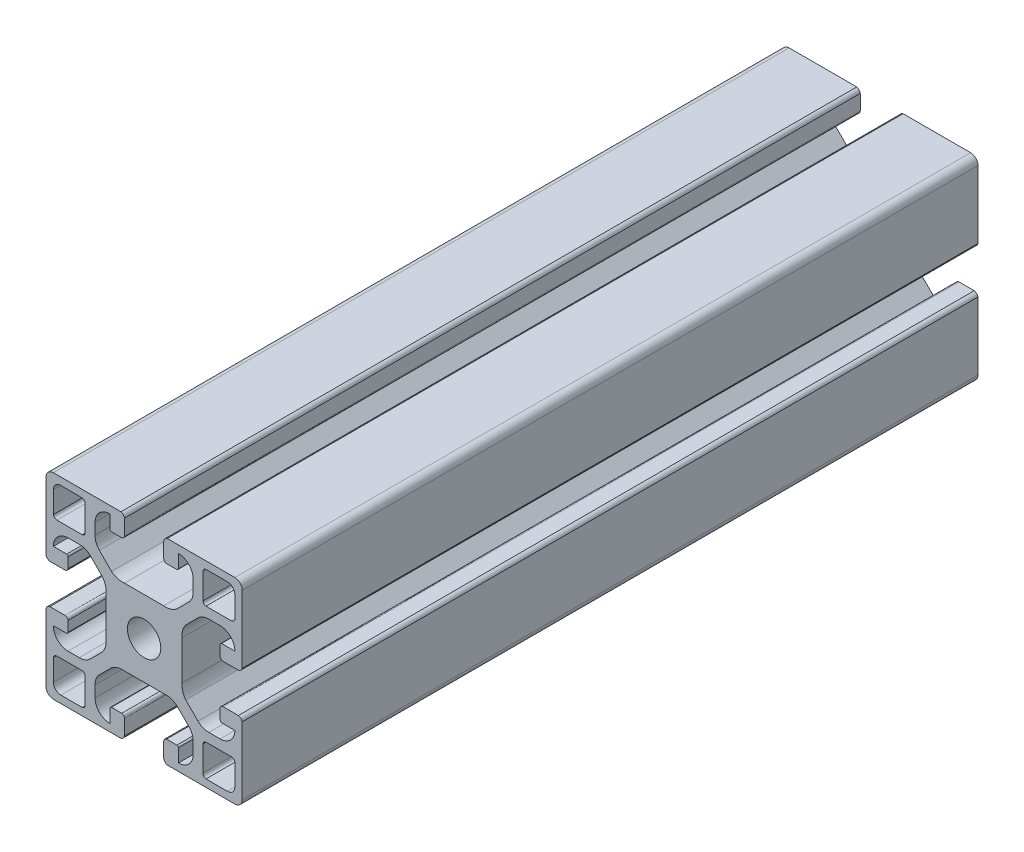
SolidWorks part; units mm, degrees
ref_plane "Alzado" through (0, 0, 0) normal (0, 0, 1) x (1, 0, 0)
ref_plane "Planta" through (0, 0, 0) normal (0, 1, 0) x (1, 0, 0)
ref_plane "Vista lateral" through (0, 0, 0) normal (1, 0, 0) x (0, 0, -1)
sketch "Croquis1" plane through (0, 0, 0) normal (0, 0, 1) x (1, 0, 0)
  line L9 (0, 18.5) -> (0, 4.7232)
  line L10 (0.7765, 4) -> (3.8765, 4)
  line L12 (12.25, -4.7232) -> (12.25, 4.7232)
  line L14 (4.5, 4.5616) -> (4.5, 6.6755)
  line L15 (4.2267, 7) -> (1.5, 7)
  line L17 (9.0164, 9.1211) -> (11.5076, 6.6299)
  line L18 (6.9331, 10) -> (4.5, 10)
  line L19 (40, -18.5) -> (40, -4.7232)
  line L20 (5.7166, 12) -> (7.3817, 12)
  line L21 (5.7166, 12) -> (2.23, 12)
  line L22 (1.5, 12.6183) -> (1.5, 17)
  line L23 (24.7232, 7.75) -> (15.2768, 7.75)
  line L24 (10.8789, 10.9836) -> (13.3701, 8.4924)
  line L25 (10, 13.0669) -> (10, 15.5)
  line L26 (13, 15.7733) -> (13, 18.5)
  line L27 (15.4384, 15.5) -> (13.3245, 15.5)
  line L28 (16, 19.2235) -> (16, 16.1235)
  line L29 (1.3293, 20) -> (15.2768, 20)
  line L30 (8, 14.2834) -> (8, 12.6183)
  line L31 (8, 14.2834) -> (8, 17.77)
  line L32 (7.3817, 18.5) -> (3, 18.5)
  line L33 (32.6183, 18.5) -> (37, 18.5)
  line L34 (32, 14.2834) -> (32, 17.77)
  line L35 (32, 14.2834) -> (32, 12.6183)
  line L36 (38.6707, 20) -> (24.7232, 20)
  line L37 (24, 19.2235) -> (24, 16.1235)
  line L38 (24.5616, 15.5) -> (26.6755, 15.5)
  line L39 (27, 15.7733) -> (27, 18.5)
  line L40 (30, 13.0669) -> (30, 15.5)
  line L41 (29.1211, 10.9836) -> (26.6299, 8.4924)
  line L42 (38.5, 12.6183) -> (38.5, 17)
  line L43 (34.2834, 12) -> (37.77, 12)
  line L44 (34.2834, 12) -> (32.6183, 12)
  line L45 (33.0669, 10) -> (35.5, 10)
  line L46 (30.9836, 9.1211) -> (28.4924, 6.6299)
  line L47 (35.7733, 7) -> (38.5, 7)
  line L48 (35.5, 4.5616) -> (35.5, 6.6755)
  line L49 (27.75, -4.7232) -> (27.75, 4.7232)
  line L51 (39.2235, 4) -> (36.1235, 4)
  line L52 (40, 18.5) -> (40, 4.7232)
  line L53 (39.2235, -4) -> (36.1235, -4)
  line L54 (35.5, -4.5616) -> (35.5, -6.6755)
  line L55 (35.7733, -7) -> (38.5, -7)
  line L56 (30.9836, -9.1211) -> (28.4924, -6.6299)
  line L57 (33.0669, -10) -> (35.5, -10)
  line L58 (34.2834, -12) -> (32.6183, -12)
  line L59 (34.2834, -12) -> (37.77, -12)
  line L60 (38.5, -12.6183) -> (38.5, -17)
  line L61 (29.1211, -10.9836) -> (26.6299, -8.4924)
  line L62 (30, -13.0669) -> (30, -15.5)
  line L63 (27, -15.7733) -> (27, -18.5)
  line L64 (24.5616, -15.5) -> (26.6755, -15.5)
  line L65 (24, -19.2235) -> (24, -16.1235)
  line L66 (38.6707, -20) -> (24.7232, -20)
  line L67 (32, -14.2834) -> (32, -12.6183)
  line L68 (32, -14.2834) -> (32, -17.77)
  line L69 (32.6183, -18.5) -> (37, -18.5)
  line L70 (7.3817, -18.5) -> (3, -18.5)
  line L71 (8, -14.2834) -> (8, -17.77)
  line L72 (8, -14.2834) -> (8, -12.6183)
  line L73 (1.3293, -20) -> (15.2768, -20)
  line L74 (16, -19.2235) -> (16, -16.1235)
  line L75 (15.4384, -15.5) -> (13.3245, -15.5)
  line L76 (13, -15.7733) -> (13, -18.5)
  line L77 (10, -13.0669) -> (10, -15.5)
  line L78 (10.8789, -10.9836) -> (13.3701, -8.4924)
  line L79 (24.7232, -7.75) -> (15.2768, -7.75)
  line L80 (1.5, -12.6183) -> (1.5, -17)
  line L81 (5.7166, -12) -> (2.23, -12)
  line L82 (5.7166, -12) -> (7.3817, -12)
  line L83 (6.9331, -10) -> (4.5, -10)
  line L84 (9.0164, -9.1211) -> (11.5076, -6.6299)
  line L85 (4.2267, -7) -> (1.5, -7)
  line L86 (4.5, -4.5616) -> (4.5, -6.6755)
  line L87 (0.7765, -4) -> (3.8765, -4)
  line L88 (0, -18.5) -> (0, -4.7232)
  arc A0 (4.5, 10) -> (1.5, 7) centre (4.5, 7) ccw
  arc A1 (10, 15.5) -> (13, 18.5) centre (13, 15.5) cw
  arc A2 (0, 18.5) -> (1.5, 20) centre (1.5, 18.5) cw
  arc A3 (1.5, 17) -> (3, 18.5) centre (3, 17) cw
  circle A4 centre (20, 0) radius 3.4
  arc A5 (38.5, 17) -> (37, 18.5) centre (37, 17) ccw
  arc A6 (40, 18.5) -> (38.5, 20) centre (38.5, 18.5) ccw
  arc A7 (30, 15.5) -> (27, 18.5) centre (27, 15.5) ccw
  arc A8 (35.5, 10) -> (38.5, 7) centre (35.5, 7) cw
  arc A9 (35.5, -10) -> (38.5, -7) centre (35.5, -7) ccw
  arc A10 (30, -15.5) -> (27, -18.5) centre (27, -15.5) cw
  arc A11 (40, -18.5) -> (38.5, -20) centre (38.5, -18.5) cw
  arc A12 (38.5, -17) -> (37, -18.5) centre (37, -17) cw
  arc A13 (1.5, -17) -> (3, -18.5) centre (3, -17) ccw
  arc A14 (0, -18.5) -> (1.5, -20) centre (1.5, -18.5) ccw
  arc A15 (10, -15.5) -> (13, -18.5) centre (13, -15.5) ccw
  arc A16 (4.5, -10) -> (1.5, -7) centre (4.5, -7) cw
  spline S0 degree 2 poles (6.7957, 10) (8.0801, 10.025) (9.0164, 9.1211) knots 0 0 0 1 1 1
  spline S1 degree 2 poles (11.5076, 6.6299) (12.3742, 5.4854) (12.25, 4) knots 0 0 0 1 1 1
  spline S2 degree 2 poles (0, 4.7232) (0.1682, 4.1542) (0.7765, 4) knots 0 0 0 1 1 1
  spline S3 degree 2 poles (3.8765, 4) (4.593, 4.0978) (4.5, 4.8884) knots 0 0 0 1 1 1
  spline S4 degree 2 poles (4.2267, 7) (4.4426, 6.908) (4.5, 6.6755) knots 0 0 0 1 1 1
  spline S5 degree 2 poles (13.3701, 8.4924) (14.5146, 7.6258) (16, 7.75) knots 0 0 0 1 1 1
  spline S6 degree 2 poles (10, 13.2043) (9.975, 11.9199) (10.8789, 10.9836) knots 0 0 0 1 1 1
  spline S7 degree 2 poles (13, 15.7733) (13.092, 15.5574) (13.3245, 15.5) knots 0 0 0 1 1 1
  spline S8 degree 2 poles (16, 16.1235) (15.9022, 15.407) (15.1116, 15.5) knots 0 0 0 1 1 1
  spline S9 degree 2 poles (15.2768, 20) (15.8458, 19.8318) (16, 19.2235) knots 0 0 0 1 1 1
  spline S10 degree 2 poles (1.5, 12.6183) (1.6133, 12.0451) (2.23, 12) knots 0 0 0 1 1 1
  spline S11 degree 2 poles (7.3817, 18.5) (7.9549, 18.3867) (8, 17.77) knots 0 0 0 1 1 1
  spline S12 degree 2 poles (7.3817, 12) (7.9101, 12.0752) (8, 12.6183) knots 0 0 0 1 1 1
  spline S13 degree 2 poles (32.6183, 12) (32.0899, 12.0752) (32, 12.6183) knots 0 0 0 1 1 1
  spline S14 degree 2 poles (32.6183, 18.5) (32.0451, 18.3867) (32, 17.77) knots 0 0 0 1 1 1
  spline S15 degree 2 poles (38.5, 12.6183) (38.3867, 12.0451) (37.77, 12) knots 0 0 0 1 1 1
  spline S16 degree 2 poles (24.7232, 20) (24.1542, 19.8318) (24, 19.2235) knots 0 0 0 1 1 1
  spline S17 degree 2 poles (24, 16.1235) (24.0978, 15.407) (24.8884, 15.5) knots 0 0 0 1 1 1
  spline S18 degree 2 poles (27, 15.7733) (26.908, 15.5574) (26.6755, 15.5) knots 0 0 0 1 1 1
  spline S19 degree 2 poles (30, 13.2043) (30.025, 11.9199) (29.1211, 10.9836) knots 0 0 0 1 1 1
  spline S20 degree 2 poles (26.6299, 8.4924) (25.4854, 7.6258) (24, 7.75) knots 0 0 0 1 1 1
  spline S21 degree 2 poles (35.7733, 7) (35.5574, 6.908) (35.5, 6.6755) knots 0 0 0 1 1 1
  spline S22 degree 2 poles (36.1235, 4) (35.407, 4.0978) (35.5, 4.8884) knots 0 0 0 1 1 1
  spline S23 degree 2 poles (40, 4.7232) (39.8318, 4.1542) (39.2235, 4) knots 0 0 0 1 1 1
  spline S24 degree 2 poles (28.4924, 6.6299) (27.6258, 5.4854) (27.75, 4) knots 0 0 0 1 1 1
  spline S25 degree 2 poles (33.2043, 10) (31.9199, 10.025) (30.9836, 9.1211) knots 0 0 0 1 1 1
  spline S26 degree 2 poles (33.2043, -10) (31.9199, -10.025) (30.9836, -9.1211) knots 0 0 0 1 1 1
  spline S27 degree 2 poles (28.4924, -6.6299) (27.6258, -5.4854) (27.75, -4) knots 0 0 0 1 1 1
  spline S28 degree 2 poles (40, -4.7232) (39.8318, -4.1542) (39.2235, -4) knots 0 0 0 1 1 1
  spline S29 degree 2 poles (36.1235, -4) (35.407, -4.0978) (35.5, -4.8884) knots 0 0 0 1 1 1
  spline S30 degree 2 poles (35.7733, -7) (35.5574, -6.908) (35.5, -6.6755) knots 0 0 0 1 1 1
  spline S31 degree 2 poles (26.6299, -8.4924) (25.4854, -7.6258) (24, -7.75) knots 0 0 0 1 1 1
  spline S32 degree 2 poles (30, -13.2043) (30.025, -11.9199) (29.1211, -10.9836) knots 0 0 0 1 1 1
  spline S33 degree 2 poles (27, -15.7733) (26.908, -15.5574) (26.6755, -15.5) knots 0 0 0 1 1 1
  spline S34 degree 2 poles (24, -16.1235) (24.0978, -15.407) (24.8884, -15.5) knots 0 0 0 1 1 1
  spline S35 degree 2 poles (24.7232, -20) (24.1542, -19.8318) (24, -19.2235) knots 0 0 0 1 1 1
  spline S36 degree 2 poles (38.5, -12.6183) (38.3867, -12.0451) (37.77, -12) knots 0 0 0 1 1 1
  spline S37 degree 2 poles (32.6183, -18.5) (32.0451, -18.3867) (32, -17.77) knots 0 0 0 1 1 1
  spline S38 degree 2 poles (32.6183, -12) (32.0899, -12.0752) (32, -12.6183) knots 0 0 0 1 1 1
  spline S39 degree 2 poles (7.3817, -12) (7.9101, -12.0752) (8, -12.6183) knots 0 0 0 1 1 1
  spline S40 degree 2 poles (7.3817, -18.5) (7.9549, -18.3867) (8, -17.77) knots 0 0 0 1 1 1
  spline S41 degree 2 poles (1.5, -12.6183) (1.6133, -12.0451) (2.23, -12) knots 0 0 0 1 1 1
  spline S42 degree 2 poles (15.2768, -20) (15.8458, -19.8318) (16, -19.2235) knots 0 0 0 1 1 1
  spline S43 degree 2 poles (16, -16.1235) (15.9022, -15.407) (15.1116, -15.5) knots 0 0 0 1 1 1
  spline S44 degree 2 poles (13, -15.7733) (13.092, -15.5574) (13.3245, -15.5) knots 0 0 0 1 1 1
  spline S45 degree 2 poles (10, -13.2043) (9.975, -11.9199) (10.8789, -10.9836) knots 0 0 0 1 1 1
  spline S46 degree 2 poles (13.3701, -8.4924) (14.5146, -7.6258) (16, -7.75) knots 0 0 0 1 1 1
  spline S47 degree 2 poles (4.2267, -7) (4.4426, -6.908) (4.5, -6.6755) knots 0 0 0 1 1 1
  spline S48 degree 2 poles (3.8765, -4) (4.593, -4.0978) (4.5, -4.8884) knots 0 0 0 1 1 1
  spline S49 degree 2 poles (0, -4.7232) (0.1682, -4.1542) (0.7765, -4) knots 0 0 0 1 1 1
  spline S50 degree 2 poles (11.5076, -6.6299) (12.3742, -5.4854) (12.25, -4) knots 0 0 0 1 1 1
  spline S51 degree 2 poles (6.7957, -10) (8.0801, -10.025) (9.0164, -9.1211) knots 0 0 0 1 1 1
extrude "Saliente-Extruir1" add sketch "Croquis1" along normal blind 150 contours S51 L83 A16 L85 S47 L86 S48 L87 S49 L88 A14 L73 S42 L74 S43 L75 S44 L76 A15 L77 S45 L78 S46 L79 S31 L61 S32 L62 A10 L63 S33 L64 S34 L65 S35 L66 A11 L19 S28 L53 S29 L54 S30
